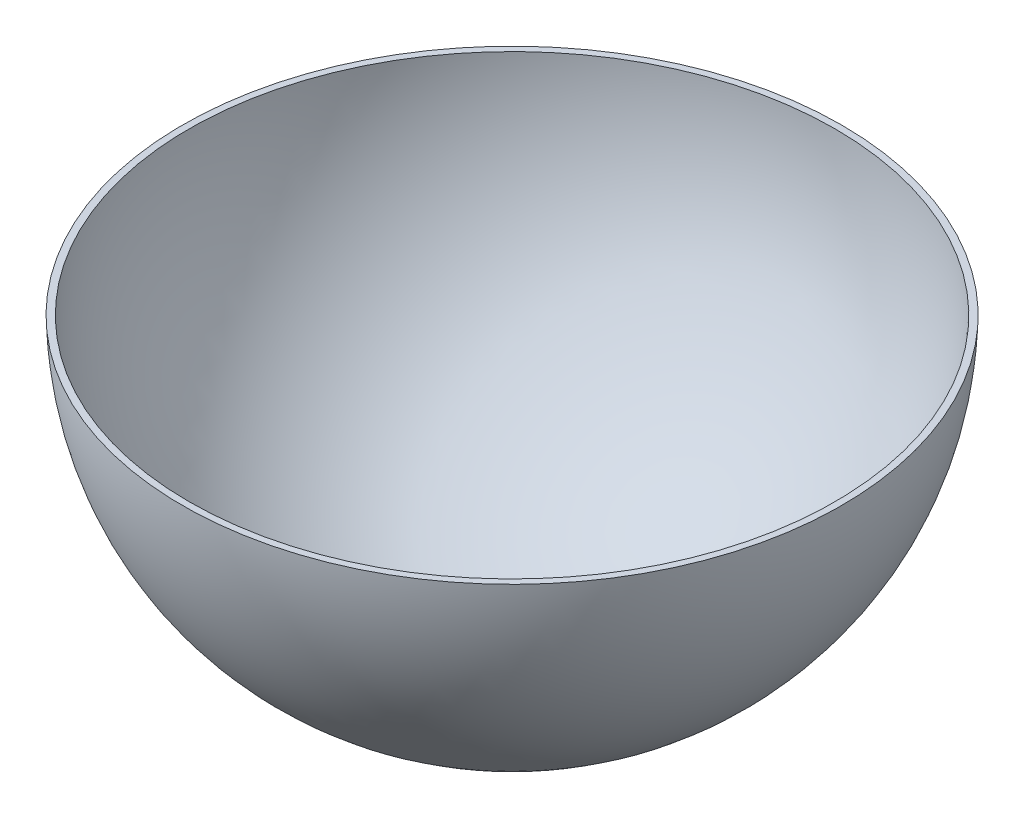
SolidWorks part; units mm, degrees
ref_plane "Front Plane" through (0, 0, 0) normal (0, 0, 1) x (1, 0, 0)
ref_plane "Top Plane" through (0, 0, 0) normal (0, 1, 0) x (1, 0, 0)
ref_plane "Right Plane" through (0, 0, 0) normal (1, 0, 0) x (0, 0, -1)
sketch "Sketch1" plane through (0, 0, 0) normal (1, 0, 0) x (0, 0, -1)
  line L0 (0, 125) -> (0, -125)
  circle A0 centre (0, 0) radius 125
  circle A1 centre (0, 0) radius 122.5
  dimension "D1" = 250
  dimension "D2" = 245
revolve "Revolve1" add sketch "Sketch1" angle 360 about L0
sketch "Sketch2" plane through (0, 0, 0) normal (0, 0, 1) x (1, 0, 0)
  line L1 (-160.6226, 162.4244) -> (168.8596, 162.4244)
  line L2 (-160.6226, 162.4244) -> (-160.6226, -3.1938)
  line L3 (-160.6226, -3.1938) -> (168.8596, -3.1938)
  line L4 (168.8596, 162.4244) -> (168.8596, -3.1938)
extrude "Cut-Extrude1" cut sketch "Sketch2" against normal through all both and the other way through all
